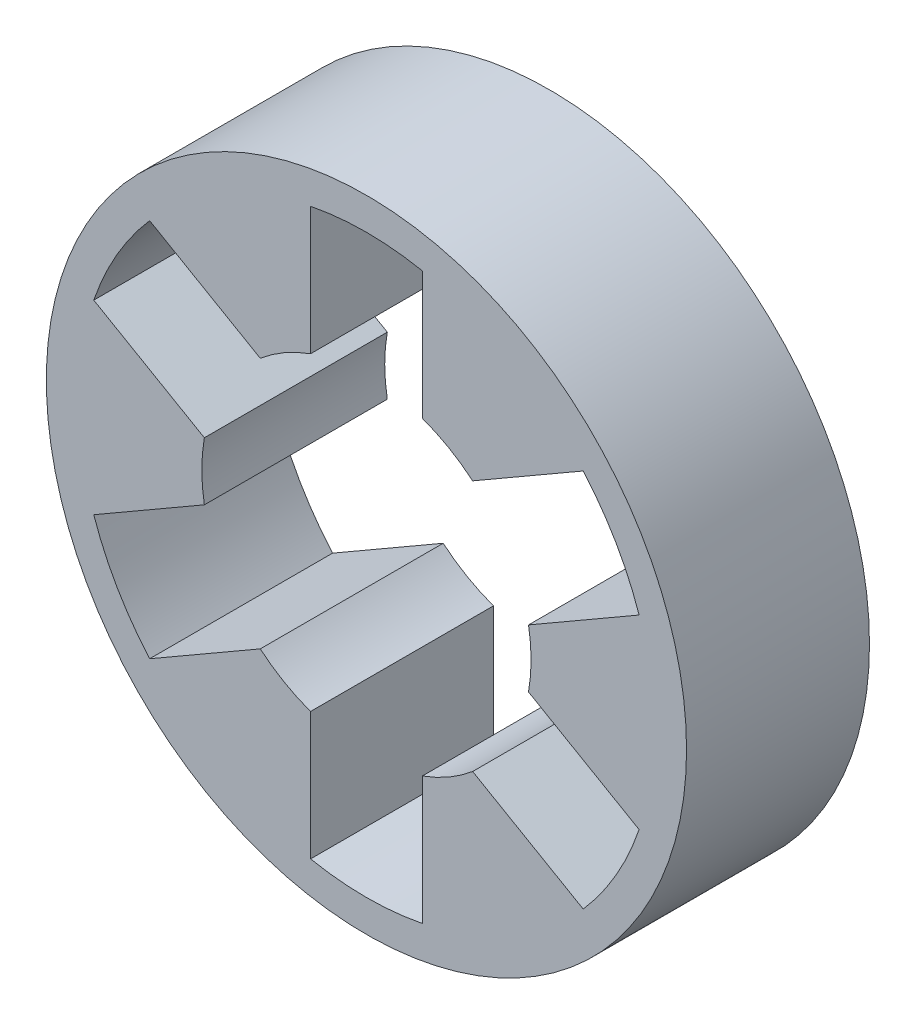
SolidWorks part; units mm, degrees
ref_plane "Front Plane" through (0, 0, 0) normal (0, 0, 1) x (1, 0, 0)
ref_plane "Top Plane" through (0, 0, 0) normal (0, 1, 0) x (1, 0, 0)
ref_plane "Right Plane" through (0, 0, 0) normal (1, 0, 0) x (0, 0, -1)
sketch "Sketch1" plane through (0, 0, 0) normal (0, 0, 1) x (1, 0, 0)
  circle A0 centre (0, 0) radius 27.7813
  circle A1 centre (0, 0) radius 14.29
  dimension "D1" = 55.5625
extrude "Boss-Extrude1" add sketch "Sketch1" along normal blind 15.875
sketch "Sketch3" plane through (0, 0, 15.875) normal (0, 0, 1) x (1, 0, 0)
  line L0 (18.8143, -16.4627) -> (4.85, -8.4004)
  line L2 (4.85, 24.525) -> (4.85, 8.4004)
  line L4 (-4.85, 24.525) -> (-4.85, 8.4004)
  line L5 (23.6643, -8.0623) -> (9.7, 0)
  line L6 (-23.6643, -8.0623) -> (-9.7, 0)
  line L7 (-18.8143, -16.4627) -> (-4.85, -8.4004)
  line L8 (4.85, 8.4004) -> (18.8143, 16.4627)
  line L9 (-4.85, 8.4004) -> (-18.8143, 16.4627)
  line L10 (-4.85, -8.4004) -> (-4.85, -24.525)
  line L13 (9.7, 0) -> (23.6643, 8.0623)
  line L14 (4.85, -8.4004) -> (4.85, -24.525)
  line L15 (-9.7, 0) -> (-23.6643, 8.0623)
  arc A0 (-23.6643, -8.0623) -> (-18.8143, -16.4627) centre (0, 0) ccw
  arc A1 (-18.8143, 16.4627) -> (-23.6643, 8.0623) centre (0, 0) ccw
  arc A2 (4.85, 24.525) -> (-4.85, 24.525) centre (0, 0) ccw
  arc A3 (23.6643, 8.0623) -> (18.8143, 16.4627) centre (0, 0) ccw
  arc A4 (18.8143, -16.4627) -> (23.6643, -8.0623) centre (0, 0) ccw
  arc A5 (-4.85, -24.525) -> (4.85, -24.525) centre (0, 0) ccw
  dimension "D1" = 3
  dimension "D2" = 4.85
extrude "Cut-Extrude1" cut sketch "Sketch3" against normal through all
